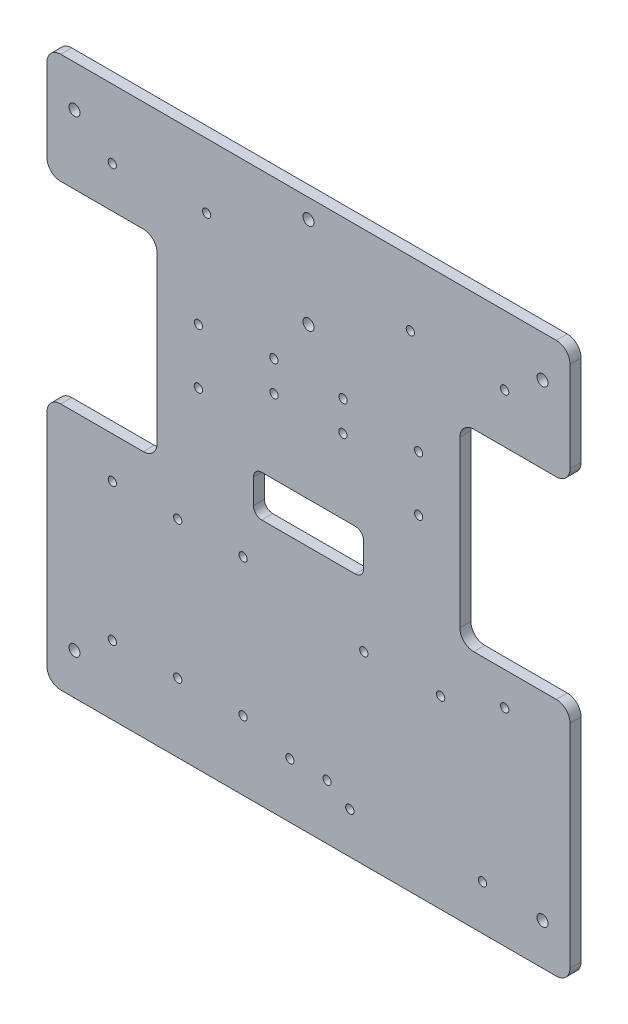
SolidWorks part; units mm, degrees
ref_plane "Front" through (0, 0, 0) normal (0, 0, 1) x (1, 0, 0)
ref_plane "Top" through (0, 0, 0) normal (0, 1, 0) x (1, 0, 0)
ref_plane "Right" through (0, 0, 0) normal (1, 0, 0) x (0, 0, -1)
sketch "Sketch1" plane through (0, 0, 0) normal (0, 0, 1) x (1, 0, 0)
  line L0 (-95, -115) -> (-95, -195)
  line L1 (-90, 0) -> (90, 0)
  line L2 (-95, -5) -> (-95, -35)
  line L3 (-90, -200) -> (90, -200)
  line L4 (95, -5) -> (95, -37.9398)
  line L5 (-90, -40) -> (-60, -40)
  line L7 (-90, -110) -> (-60, -110)
  line L8 (-55, -45) -> (-55, -105)
  line L9 (90, -42.9398) -> (60, -42.9398)
  line L11 (90, -112.9398) -> (60, -112.9398)
  line L12 (55, -47.9398) -> (55, -107.9398)
  line L13 (95, -117.9398) -> (95, -195)
  arc A0 (-95, -195) -> (-90, -200) centre (-90, -195) ccw
  arc A1 (95, -5) -> (90, 0) centre (90, -5) ccw
  arc A2 (-90, 0) -> (-95, -5) centre (-90, -5) ccw
  arc A3 (90, -200) -> (95, -195) centre (90, -195) ccw
  arc A4 (95, -37.9398) -> (90, -42.9398) centre (90, -37.9398) cw
  arc A5 (95, -117.9398) -> (90, -112.9398) centre (90, -117.9398) ccw
  arc A6 (60, -42.9398) -> (55, -47.9398) centre (60, -47.9398) ccw
  arc A7 (60, -112.9398) -> (55, -107.9398) centre (60, -107.9398) cw
  arc A8 (-95, -115) -> (-90, -110) centre (-90, -115) cw
  arc A9 (-60, -110) -> (-55, -105) centre (-60, -105) ccw
  arc A10 (-60, -40) -> (-55, -45) centre (-60, -45) cw
  arc A11 (-90, -40) -> (-95, -35) centre (-90, -35) cw
  point P4 (0, 0)
  point P10 (95, 0)
  point P13 (-95, 0)
  point P16 (95, -200)
  point P27 (95, -42.9398)
  point P32 (55, -42.9398)
  point P35 (55, -112.9398)
  point P40 (-55, -110)
  point P43 (-55, -40)
  point P46 (-95, -40)
  dimension "D3" = 5
  dimension "D4" = 5
  dimension "D5" = 5
  dimension "D6" = 5
  dimension "D12" = 5
  dimension "D1" = 190
  dimension "D2" = 200
  dimension "D7" = 40
  dimension "D8" = 40
  dimension "D9" = 40
  dimension "D10" = 70
  dimension "D11" = 70
extrude "Boss-Extrude1" add sketch "Sketch1" along normal blind 4
sketch "Sketch2" plane through (0, 0, 4) normal (0, 0, 1) x (1, 0, 0)
  line L0 (0, -218.7659) -> (0, 71.8391) construction
  line L1 (-95, -5) -> (-95, -35) construction
  line L2 (-90, -200) -> (90, -200) construction
  line L3 (90, 0) -> (-90, 0) construction
  line L4 (-90, -200) -> (90, -200) construction
  circle A0 centre (-85, -185) radius 2
  circle A1 centre (-85, -15) radius 2
  circle A2 centre (85, -15) radius 2
  circle A3 centre (85, -185) radius 2
  circle A4 centre (-6.765, -180) radius 1.5
  circle A5 centre (6.765, -180) radius 1.5
  dimension "D1" = 4
  dimension "D2" = 4
  dimension "D7" = 13.53
  dimension "D3" = 10
  dimension "D4" = 15
  dimension "D5" = 15
  dimension "D6" = 10
  dimension "D8" = 20
extrude "Cut-Extrude1" cut sketch "Sketch2" against normal blind 20
sketch "Sketch3" plane through (0, 0, 4) normal (0, 0, 1) x (1, 0, 0)
  line L0 (0, 38.5018) -> (0, -275.6294) construction
  line L1 (-47.5, 21.4724) -> (-47.5, -234.3108) construction
  line L2 (-148.4478, -100) -> (135.558, -100) construction
  line L3 (-122.1233, -50) -> (119.5593, -50) construction
  line L4 (90, 0) -> (-90, 0) construction
  line L5 (-95, -5) -> (-95, -35) construction
  circle A0 centre (-71.25, -25) radius 1.5
  circle A1 centre (-71.25, -75) radius 1.5
  circle A2 centre (-71.25, -175) radius 1.5
  circle A3 centre (-71.25, -125) radius 1.5
  circle A12 centre (71.25, -125) radius 1.5
  circle A14 centre (71.25, -75) radius 1.5
  circle A15 centre (71.25, -25) radius 1.5
  circle A16 centre (-23.75, -125) radius 1.5
  circle A17 centre (-23.75, -175) radius 1.5
  circle A18 centre (-47.5, -125) radius 1.5
  circle A19 centre (-47.5, -175) radius 1.5
  dimension "D5" = 25
  dimension "D7" = 3
  dimension "D8" = 3
  dimension "D9" = 3
  dimension "D1" = 50
  dimension "D2" = 100
  dimension "D3" = 47.5
  dimension "D4" = 95
  dimension "D6" = 23.75
extrude "Cut-Extrude2" cut sketch "Sketch3" against normal blind 10
sketch "Sketch4" plane through (0, 0, 4) normal (0, 0, 1) x (1, 0, 0)
  line L0 (-6.765, -180) -> (6.765, -180) construction
sketch "Sketch5" plane through (0, 0, 4) normal (0, 0, 1) x (1, 0, 0)
  line L0 (0, 0) -> (0, -200) construction
  line L3 (-90, -200) -> (90, -200) construction
  line L4 (-55, -45) -> (-55, -105) construction
  line L5 (-90, -40) -> (-60, -40) construction
  line L6 (-90, -200) -> (90, -200) construction
  line L7 (90, 0) -> (-90, 0) construction
  line L8 (-37, -23.5) -> (37, -23.5) construction
  line L9 (0, -7) -> (0, -40) construction
  circle A4 centre (-40, -60) radius 1.5
  circle A5 centre (-40, -80) radius 1.5
  circle A6 centre (40, -80) radius 1.5
  circle A7 centre (40, -60) radius 1.5
  circle A9 centre (20.1, -132.9) radius 1.5
  circle A10 centre (15, -185) radius 1.5
  circle A11 centre (63.2, -183.7) radius 1.5
  circle A13 centre (48, -132.9) radius 1.5
  circle A14 centre (0, -7) radius 2
  circle A15 centre (0, -40) radius 2
  circle A16 centre (-37, -23.5) radius 1.5
  circle A17 centre (37, -23.5) radius 1.5
  point P42 (0, -23.5)
  point P44 (0, -23.5)
  dimension "D2" = 3
  dimension "D3" = 3
  dimension "D4" = 3
  dimension "D5" = 3
  dimension "D9" = 50.8
  dimension "D11" = 3
  dimension "D13" = 3
  dimension "D16" = 20
  dimension "D17" = 20
  dimension "D7" = 15.2
  dimension "D8" = 5.1
  dimension "D10" = 52.1
  dimension "D19" = 4
  dimension "D20" = 4
  dimension "D21" = 33
  dimension "D22" = 7
  dimension "D23" = 37
  dimension "D24" = 3
  dimension "D25" = 3
  dimension "D6" = 27.9
  dimension "D12" = 15
  dimension "D14" = 15
  dimension "D15" = 15
  dimension "D18" = 15
extrude "Cut-Extrude3" cut sketch "Sketch5" against normal through all
sketch "Sketch7" plane through (0, 0, 0) normal (0, 0, -1) x (-1, 0, 0)
  line L0 (0, 20.9768) -> (0, -223.1934) construction
  line L1 (-90, 0) -> (90, 0) construction
  line L2 (17, -110) -> (-17, -110)
  line L3 (20, -107) -> (20, -98)
  line L4 (17, -95) -> (-17, -95)
  line L5 (-20, -107) -> (-20, -98)
  circle A0 centre (12.5687, -57.036) radius 1.5
  circle A1 centre (12.5, -68.0358) radius 1.5
  circle A2 centre (-12.5, -68.0358) radius 1.5
  circle A3 centre (-12.5687, -57.036) radius 1.5
  arc A4 (-17, -110) -> (-20, -107) centre (-17, -107) cw
  arc A5 (-17, -95) -> (-20, -98) centre (-17, -98) ccw
  arc A6 (20, -98) -> (17, -95) centre (17, -98) ccw
  arc A7 (17, -110) -> (20, -107) centre (17, -107) ccw
  point P15 (0, -110)
  point P20 (-20, -110)
  point P23 (-20, -95)
  point P28 (20, -110)
  dimension "D1" = 3
  dimension "D2" = 3
  dimension "D8" = 3
  dimension "D3" = 11
  dimension "D4" = 12.5
  dimension "D5" = 40
  dimension "D6" = 15
  dimension "D7" = 110
extrude "Cut-Extrude4" cut sketch "Sketch7" against normal blind 10
